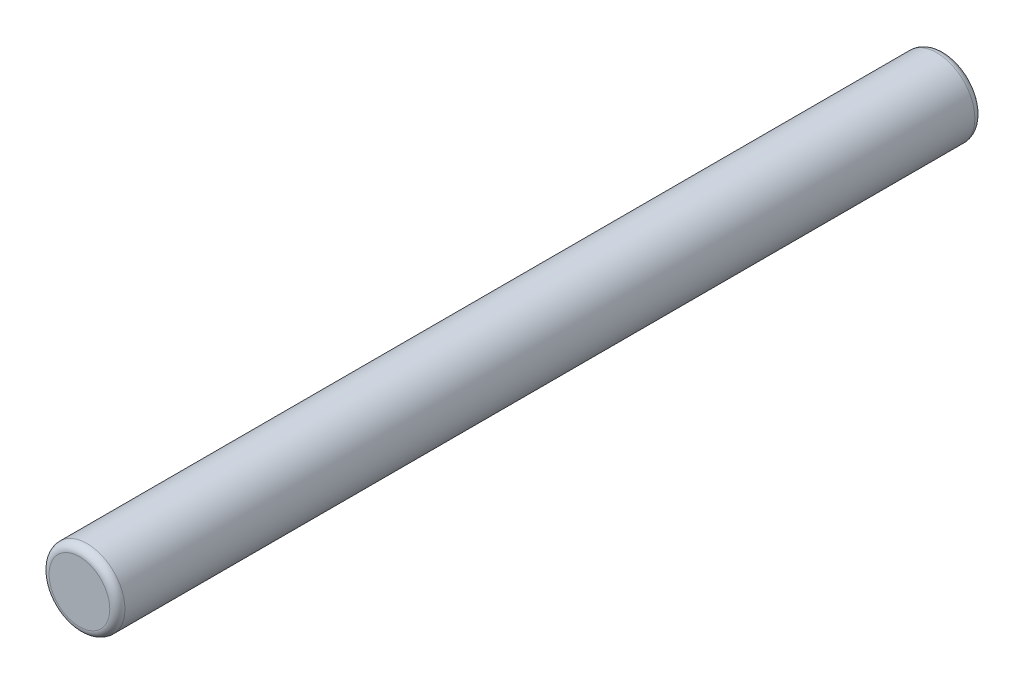
SolidWorks part; units mm, degrees
ref_plane "Front" through (0, 0, 0) normal (0, 0, 1) x (1, 0, 0)
ref_plane "Top" through (0, 0, 0) normal (0, 1, 0) x (1, 0, 0)
ref_plane "Right" through (0, 0, 0) normal (1, 0, 0) x (0, 0, -1)
sketch "Sketch1" plane through (0, 0, 0) normal (0, 0, 1) x (1, 0, 0)
  circle A0 centre (0, 0) radius 2.5
  dimension "D1" = 5
extrude "Boss-Extrude1" add sketch "Sketch1" along normal blind 57
fillet "Fillet2" radius 0.5 1 edges at (2.5, 0, 0)
fillet "Fillet3" radius 0.5 1 edges at (2.5, 0, 57)
